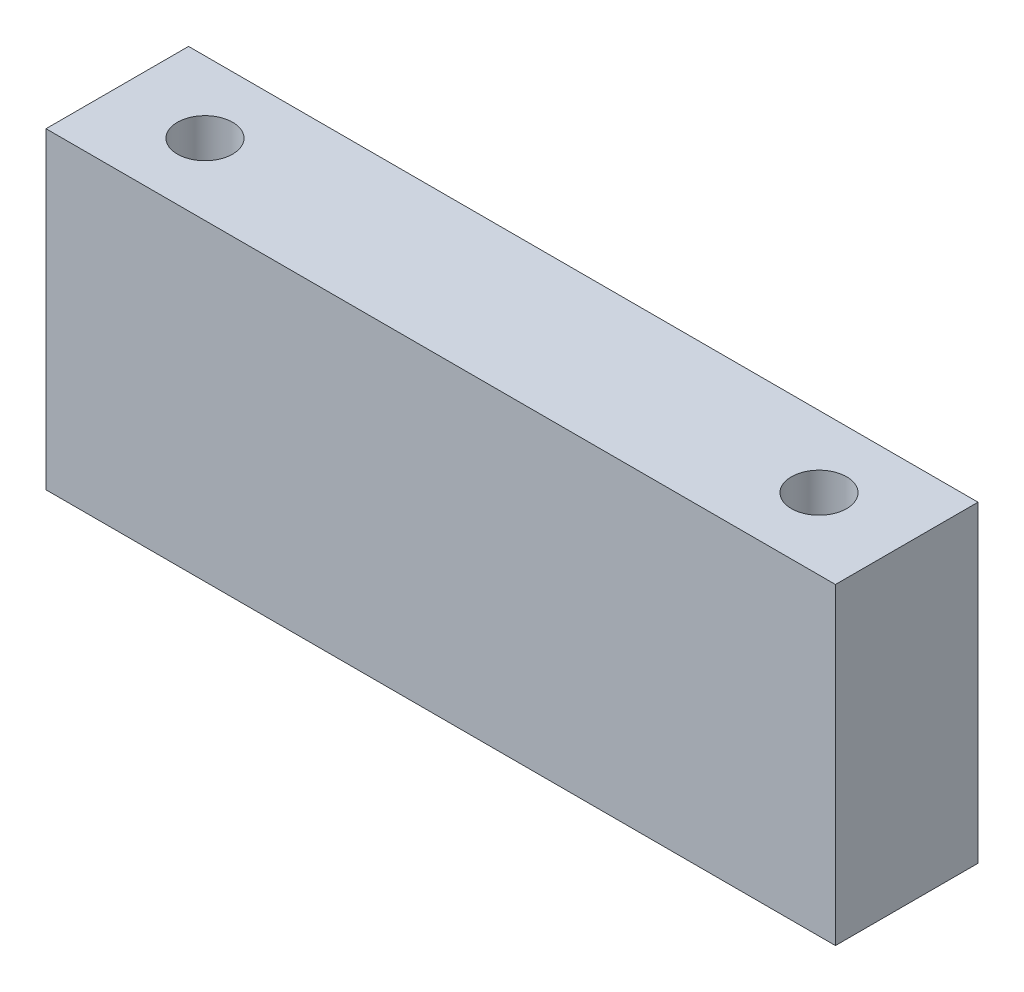
SolidWorks part; units mm, degrees
ref_plane "Front Plane" through (0, 0, 0) normal (0, 0, 1) x (1, 0, 0)
ref_plane "Top Plane" through (0, 0, 0) normal (0, 1, 0) x (1, 0, 0)
ref_plane "Right Plane" through (0, 0, 0) normal (1, 0, 0) x (0, 0, -1)
sketch "Sketch1" plane through (0, 0, 0) normal (0, 1, 0) x (1, 0, 0)
  line L0 (-22.225, 0) -> (22.225, 0) construction
  line L1 (-28.575, -5.16) -> (28.575, -5.16)
  line L2 (-28.575, -5.16) -> (-28.575, 5.16)
  line L3 (-28.575, 5.16) -> (28.575, 5.16)
  line L4 (28.575, -5.16) -> (28.575, 5.16)
  line L5 (-28.575, -5.16) -> (28.575, 5.16) construction
  line L6 (-28.575, 5.16) -> (28.575, -5.16) construction
  circle A0 centre (-22.225, 0) radius 2
  circle A1 centre (22.225, 0) radius 2
  point P0 (0, 0)
  dimension "D3" = 4
  dimension "D4" = 4
  dimension "D1" = 57.15
  dimension "D2" = 10.32
  dimension "D5" = 44.45
  dimension "D6" = 22.225
extrude "Boss-Extrude1" add sketch "Sketch1" along normal blind 22.64
